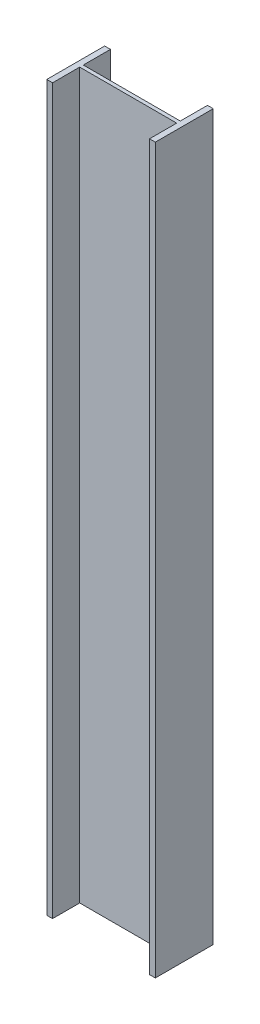
SolidWorks part; units mm, degrees
material "Plain Carbon Steel"
ref_plane "Front Plane" through (0, 0, 0) normal (0, 0, 1) x (1, 0, 0)
ref_plane "Top Plane" through (0, 0, 0) normal (0, 1, 0) x (1, 0, 0)
ref_plane "Right Plane" through (0, 0, 0) normal (1, 0, 0) x (0, 0, -1)
sketch "Sketch1" plane through (0, 0, 0) normal (0, 1, 0) x (1, 0, 0)
  line L2 (-67, 2.5) -> (-67, 40)
  line L3 (-67, 40) -> (-75, 40)
  line L4 (-75, 40) -> (-75, -40)
  line L5 (-75, -40) -> (-67, -40)
  line L6 (-67, -40) -> (-67, -2.5)
  line L7 (-67, -2.5) -> (67, -2.5)
  line L8 (67, -2.5) -> (67, -40)
  line L9 (67, -40) -> (75, -40)
  line L10 (75, -40) -> (75, 40)
  line L11 (75, 40) -> (67, 40)
  line L12 (67, 40) -> (67, 2.5)
  line L13 (67, 2.5) -> (-67, 2.5)
  dimension "D1" = 8
  dimension "D2" = 80
  dimension "D3" = 134
  dimension "D4" = 5
  dimension "D5" = 150
extrude "Boss-Extrude1" add sketch "Sketch1" along normal blind 1000
